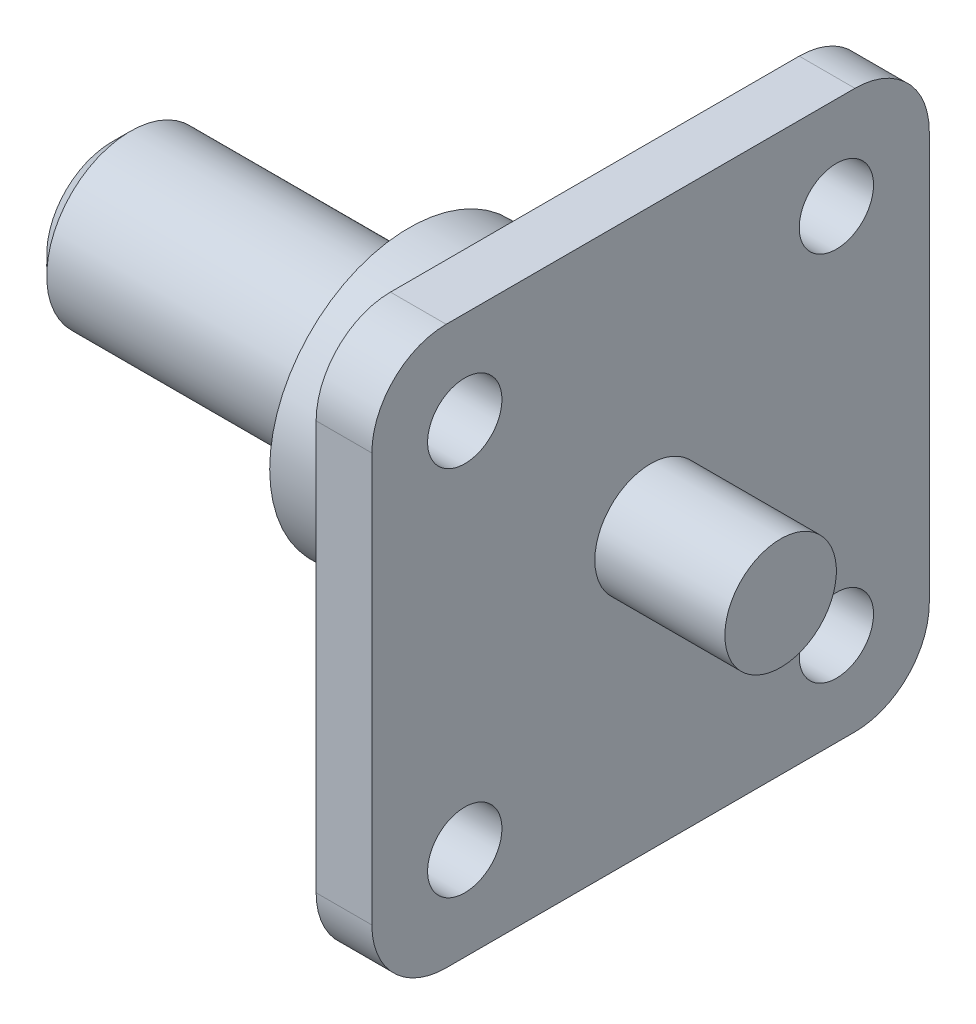
SolidWorks part; units mm, degrees
ref_plane "Alzado" through (0, 0, 0) normal (0, 0, 1) x (1, 0, 0)
ref_plane "Planta" through (0, 0, 0) normal (0, 1, 0) x (1, 0, 0)
ref_plane "Vista lateral" through (0, 0, 0) normal (1, 0, 0) x (0, 0, -1)
sketch "Croquis1" plane through (0, 0, 0) normal (0, 0, 1) x (1, 0, 0)
  line L0 (-18.3711, 0) -> (42.3295, 0) construction
  line L1 (-16, 0) -> (-16, 4.5)
  line L2 (-16, 4.5) -> (0, 4.5)
  line L3 (0, 4.5) -> (0, 7.5)
  line L4 (0, 7.5) -> (10, 7.5)
  line L5 (10, 7.5) -> (10, 0) construction
  line L6 (-16, 0) -> (20, 0)
  line L7 (10, 7.5) -> (10, 3)
  line L8 (10, 3) -> (20, 3)
  line L9 (20, 3) -> (20, 0)
  line L10 (0, 0) -> (0, 8.1876) construction
  point P9 (0, 6)
  dimension "D1" = 9
  dimension "D2" = 15
  dimension "D3" = 16
  dimension "D4" = 10
  dimension "D5" = 6
  dimension "D6" = 10
revolve "Revolución1" add sketch "Croquis1" angle 360 about L0
fillet "Redondeo1" radius 1 1 edges at (0, 0, 4.5)
chamfer "Chaflán1" distance 1 angle 45 1 edges at (-16, 0, 4.5)
sketch "Croquis2" plane through (10, 0, 0) normal (1, 0, 0) x (0, 0, -1)
  line L1 (-11, -15) -> (11, -15)
  line L2 (-15, -11) -> (-15, 11)
  line L3 (-11, 15) -> (11, 15)
  line L4 (15, -11) -> (15, 11)
  line L5 (-15, -15) -> (15, 15) construction
  line L6 (-15, 15) -> (15, -15) construction
  line L7 (-10, -10) -> (10, -10) construction
  line L8 (-10, -10) -> (-10, 10) construction
  line L9 (-10, 10) -> (10, 10) construction
  line L10 (10, -10) -> (10, 10) construction
  line L11 (-10, -10) -> (10, 10) construction
  line L12 (-10, 10) -> (10, -10) construction
  circle A0 centre (-10, 10) radius 2
  circle A1 centre (10, 10) radius 2
  circle A2 centre (10, -10) radius 2
  circle A3 centre (-10, -10) radius 2
  arc A4 (-11, -15) -> (-15, -11) centre (-11, -11) cw
  arc A5 (11, -15) -> (15, -11) centre (11, -11) ccw
  arc A6 (11, 15) -> (15, 11) centre (11, 11) cw
  arc A7 (-15, 11) -> (-11, 15) centre (-11, 11) cw
  point P0 (0, 0)
  point P5 (0, 0)
  dimension "D4" = 4
  dimension "D5" = 4
  dimension "D1" = 30
  dimension "D2" = 30
  dimension "D3" = 20
extrude "Saliente-Extruir1" add sketch "Croquis2" along normal blind 3
